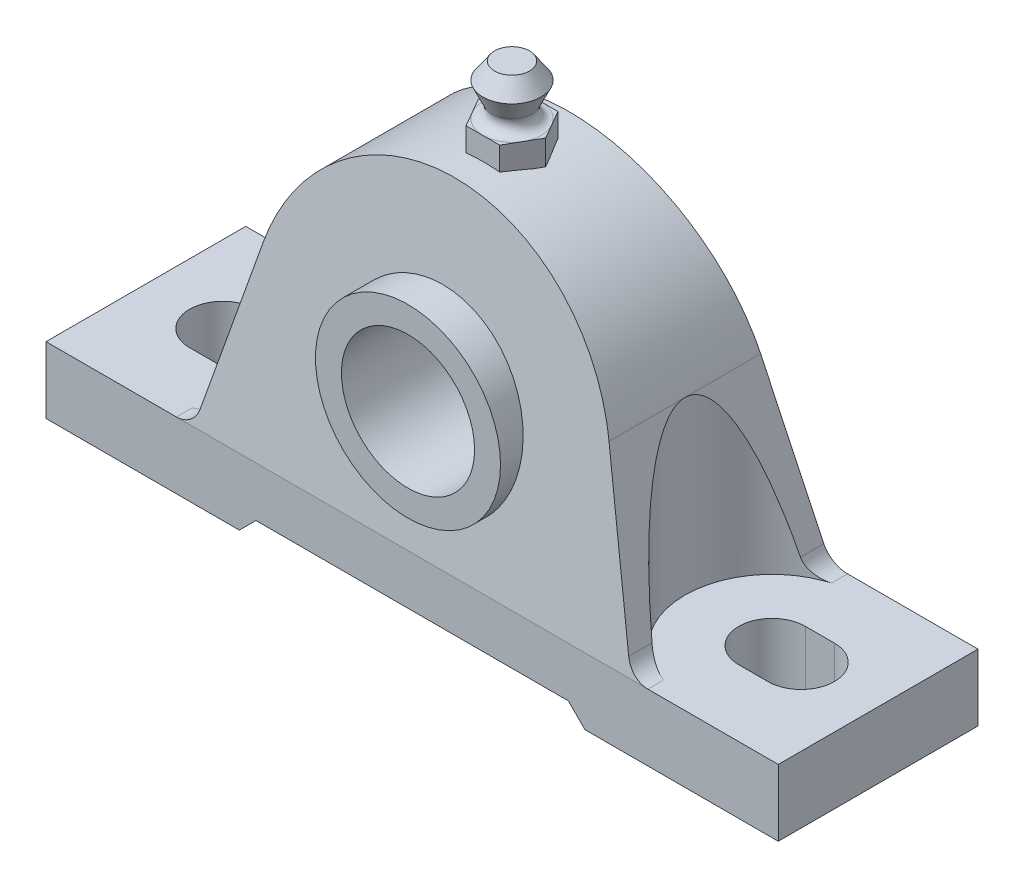
SolidWorks part; units mm, degrees
ref_plane "Front" through (0, 0, 0) normal (0, 0, 1) x (1, 0, 0)
ref_plane "Top" through (0, 0, 0) normal (0, 1, 0) x (1, 0, 0)
ref_plane "Right" through (0, 0, 0) normal (1, 0, 0) x (0, 0, -1)
sketch "Sketch1" plane through (0, 0, 0) normal (0, 0, 1) x (1, 0, 0)
  line L0 (-32.9683, 8.8338) -> (-40.8751, -20.6748) construction
  line L1 (-44.9642, -23.8125) -> (-69.85, -23.8125) construction
  line L2 (-69.85, -23.8125) -> (-69.85, -36.5125) construction
  line L3 (-69.85, -36.5125) -> (-32.9683, -36.5125) construction
  line L4 (-32.9683, -36.5125) -> (-29.7933, -33.3375) construction
  line L5 (-29.7933, -33.3375) -> (29.7933, -33.3375) construction
  line L6 (0, 0) -> (0, -41.3664) construction
  line L7 (29.7933, -33.3375) -> (32.9683, -36.5125) construction
  line L8 (32.9683, -36.5125) -> (69.85, -36.5125) construction
  line L9 (69.85, -36.5125) -> (69.85, -23.8125) construction
  line L10 (69.85, -23.8125) -> (44.9642, -23.8125) construction
  line L11 (40.8751, -20.6748) -> (32.9683, 8.8338) construction
  line L12 (-32.9683, 8.8338) -> (-32.9683, -36.5125) construction
  circle A0 centre (0, 0) radius 12.7
  circle A1 centre (0, 0) radius 17.653
  arc A2 (32.9683, 8.8338) -> (-32.9683, 8.8338) centre (0, 0) ccw construction
  arc A3 (-40.8751, -20.6748) -> (-44.9642, -23.8125) centre (-44.9642, -19.5792) cw construction
  arc A4 (44.9642, -23.8125) -> (40.8751, -20.6748) centre (44.9642, -19.5792) cw construction
  dimension "Shaft Dia" = 25.4
  dimension "C" = 35.306
  dimension "D10" = 4.2333
  dimension "D7" = 3.175
  dimension "D8" = 45
  dimension "D9" = 15
extrude "Extrude1" add sketch "Sketch1" along normal blind 19.8438 and the other way blind 14.2875
sketch "Sketch2" plane through (0, 0, 0) normal (0, 0, 1) x (1, 0, 0)
  line L0 (-32.9683, 8.8338) -> (-40.8751, -20.6748) construction
  line L1 (-44.9642, -23.8125) -> (-69.85, -23.8125) construction
  line L2 (-69.85, -23.8125) -> (-69.85, -36.5125) construction
  line L3 (-69.85, -36.5125) -> (-32.9683, -36.5125) construction
  line L4 (-32.9683, -36.5125) -> (-29.7933, -33.3375) construction
  line L5 (-29.7933, -33.3375) -> (29.7933, -33.3375) construction
  line L6 (29.7933, -33.3375) -> (32.9683, -36.5125) construction
  line L7 (32.9683, -36.5125) -> (69.85, -36.5125) construction
  line L8 (69.85, -36.5125) -> (69.85, -23.8125) construction
  line L9 (69.85, -23.8125) -> (44.9642, -23.8125) construction
  line L10 (40.8751, -20.6748) -> (32.9683, 8.8338) construction
  line L11 (-32.9683, 8.8338) -> (-40.8751, -20.6748)
  line L12 (-44.9642, -23.8125) -> (-69.85, -23.8125)
  line L13 (-69.85, -23.8125) -> (-69.85, -36.5125)
  line L14 (-69.85, -36.5125) -> (-32.9683, -36.5125)
  line L15 (-32.9683, -36.5125) -> (-29.7933, -33.3375)
  line L16 (-29.7933, -33.3375) -> (29.7933, -33.3375)
  line L17 (29.7933, -33.3375) -> (32.9683, -36.5125)
  line L18 (32.9683, -36.5125) -> (69.85, -36.5125)
  line L19 (69.85, -36.5125) -> (69.85, -23.8125)
  line L20 (69.85, -23.8125) -> (44.9642, -23.8125)
  line L21 (40.8751, -20.6748) -> (32.9683, 8.8338)
  arc A0 (-44.9642, -23.8125) -> (-40.8751, -20.6748) centre (-44.9642, -19.5792) ccw construction
  arc A1 (40.8751, -20.6748) -> (44.9642, -23.8125) centre (44.9642, -19.5792) ccw construction
  arc A2 (32.9683, 8.8338) -> (-32.9683, 8.8338) centre (0, 0) ccw construction
  arc A3 (-44.9642, -23.8125) -> (-40.8751, -20.6748) centre (-44.9642, -19.5792) ccw
  arc A4 (40.8751, -20.6748) -> (44.9642, -23.8125) centre (44.9642, -19.5792) ccw
  arc A5 (32.9683, 8.8338) -> (-32.9683, 8.8338) centre (0, 0) ccw
  circle A6 centre (0, 0) radius 17.653 construction
  circle A7 centre (0, 0) radius 17.653
extrude "Extrude2" add sketch "Sketch2" along normal mid plane 38.1 separate body
sketch "Sketch3" plane through (0, 0, 0) normal (0, 1, 0) x (1, 0, 0)
  line L0 (49.6094, 0) -> (55.1656, 0) construction
  line L1 (-49.6094, 0) -> (-55.1656, 0) construction
  line L2 (-55.1656, 6.35) -> (-49.6094, 6.35)
  line L3 (-55.1656, -6.35) -> (-49.6094, -6.35)
  line L4 (49.6094, -6.35) -> (55.1656, -6.35)
  line L5 (49.6094, 6.35) -> (55.1656, 6.35)
  line L6 (-49.6094, 0) -> (49.6094, 0) construction
  arc A0 (55.1656, 6.35) -> (55.1656, -6.35) centre (55.1656, 0) cw
  arc A1 (49.6094, 6.35) -> (49.6094, -6.35) centre (49.6094, 0) ccw
  arc A2 (-49.6094, -6.35) -> (-49.6094, 6.35) centre (-49.6094, 0) ccw
  arc A3 (-55.1656, 6.35) -> (-55.1656, -6.35) centre (-55.1656, 0) ccw
  point P13 (-52.3875, 6.35)
  point P14 (52.3875, 6.35)
  dimension "F Hole size" = 12.7
  dimension "M" = 99.2188
  dimension "M1" = 110.3312
  dimension "e" = 104.775
  dimension "S2" = 18.2562
extrude "Cut-Extrude1" cut sketch "Sketch3" against normal through all and the other way through all
sketch "Sketch4" plane through (0, 0, 0) normal (0, 1, 0) x (1, 0, 0)
  line L0 (-49.6094, 0) -> (-55.1656, 0) construction
  line L1 (49.6094, 0) -> (55.1656, 0) construction
  line L2 (-49.6094, 0) -> (-55.1656, 0) construction
  line L3 (49.6094, 0) -> (55.1656, 0) construction
  line L4 (43.7469, 15.5743) -> (69.85, 25.4)
  line L5 (69.85, 25.4) -> (69.85, -25.4)
  line L6 (69.85, -25.4) -> (43.7469, -15.5743)
  line L7 (-43.7469, -15.5743) -> (-69.85, -25.4)
  line L8 (-69.85, -25.4) -> (-69.85, 25.4)
  line L9 (-69.85, 25.4) -> (-43.7469, 15.5743)
  line L10 (69.85, -19.05) -> (69.85, 19.05) construction
  line L11 (-69.85, -19.05) -> (-69.85, 19.05) construction
  line L12 (-32.9683, -19.05) -> (-32.9683, 19.05) construction
  line L13 (0, 15.5743) -> (0, -15.5743) construction
  line L14 (0, -15.5743) -> (-43.7469, -15.5743) construction
  line L15 (-43.7469, 15.5743) -> (0, 15.5743) construction
  line L16 (-44.9642, 19.05) -> (-69.85, 19.05) construction
  arc A0 (43.7469, 15.5743) -> (43.7469, -15.5743) centre (49.6094, 0) ccw
  arc A1 (-43.7469, -15.5743) -> (-43.7469, 15.5743) centre (-49.6094, 0) ccw
  dimension "D1" = 6.35
extrude "Cut-Extrude2" cut sketch "Sketch4" against normal up to surface (23.8125 mm away) and the other way through all up to face at (-53.5036, -23.8125, 0)
sketch "Sketch5" plane through (0, 0, 0) normal (1, 0, 0) x (0, 0, -1)
  line L0 (-19.05, -23.8125) -> (-10.9065, 34.1312)
  line L1 (-10.9065, 34.1312) -> (-19.05, 34.1312)
  line L2 (-19.05, 34.1312) -> (-19.05, -23.8125)
  line L3 (-19.05, -23.8125) -> (19.05, -23.8125) construction
  line L4 (-19.05, -20.6748) -> (-19.05, 8.8338) construction
  line L5 (19.05, 34.1312) -> (-19.05, 34.1312) construction
  line L7 (-19.8438, 17.653) -> (-19.8438, -17.653) construction
  line L8 (-19.8438, 17.653) -> (-19.8438, -17.653) construction
  line L9 (14.2875, -17.653) -> (14.2875, 17.653) construction
  line L10 (14.2875, -17.653) -> (14.2875, 17.653) construction
  dimension "D1" = 8
  dimension "D2" = 34.1313
extrude "Cut-Extrude3" cut sketch "Sketch5" against normal through all and the other way through all
sketch "Sketch8" plane through (0, 0, 0) normal (1, 0, 0) x (0, 0, -1)
  line L0 (-13.2224, 17.653) -> (14.2875, 17.653) construction
  line L1 (14.2875, 17.653) -> (14.2875, -17.653) construction
  line L2 (14.2875, -17.653) -> (-18.1843, -17.653) construction
  line L3 (14.2875, -17.653) -> (14.2875, 17.653) construction
  line L4 (-19.05, -23.8125) -> (-10.9065, 34.1312) construction
mirror "Mirror1" about plane through (0, 0, 0) normal (0, 0, 1) of "Cut-Extrude3"
sketch "Sketch6" plane through (0, 0, 0) normal (0, 0, 1) x (1, 0, 0)
  line L0 (0, 0) -> (0, 34.1312) construction
  line L1 (0, 0) -> (12.7, 0) construction
  line L2 (0, 0) -> (0, 34.1312) construction
  line L4 (0, 34.1312) -> (0, 48.2689) construction
  line L5 (0, 33.676) -> (-5.5562, 33.676)
  line L6 (-5.5562, 33.676) -> (-5.5563, 38.4385)
  line L7 (-3.8466, 41.1221) -> (-5.5563, 44.7885)
  line L8 (-5.5563, 44.7885) -> (-3.3331, 47.9635)
  line L9 (-3.3331, 47.9635) -> (0, 47.9635)
  line L10 (0, 47.9635) -> (0, 33.676)
  circle A0 centre (0, 0) radius 12.7 construction
  arc A1 (32.9683, 8.8338) -> (-32.9683, 8.8338) centre (0, 0) ccw construction
  arc A2 (-5.5563, 38.4385) -> (-3.8466, 41.1221) centre (-5.5563, 40.3249) ccw
  dimension "D2" = 14.2875
  dimension "D3" = 11.1125
  dimension "D4" = 4.7625
  dimension "D5" = 55
  dimension "D6" = 3.175
  dimension "D7" = 120
revolve "Revolve1" add sketch "Sketch6" angle 360 about L4
sketch "Sketch7" plane through (0, 33.676, 0) normal (0, -1, 0) x (1, 0, 0)
  line L1 (-3.2079, 5.5563) -> (-6.4158, 0)
  line L2 (-6.4158, 0) -> (-3.2079, -5.5563)
  line L3 (-3.2079, -5.5563) -> (3.2079, -5.5563)
  line L4 (3.2079, -5.5563) -> (6.4158, 0)
  line L5 (6.4158, 0) -> (3.2079, 5.5563)
  line L6 (3.2079, 5.5563) -> (-3.2079, 5.5563)
  circle A0 centre (0, 0) radius 5.5562 construction
  circle A1 centre (0, 0) radius 5.5562 construction
extrude "Extrude3" add sketch "Sketch7" against normal up to vertex (4.7625 mm away)
equation "\"D7@Sketch1\" = \"Base Height@Sketch1\"/4"
equation "\"D10@Sketch1\"=\"Base Height@Sketch1\"/3"
equation "\"C@Sketch1\"=\"Shaft Dia@Sketch1\"*1.39"
